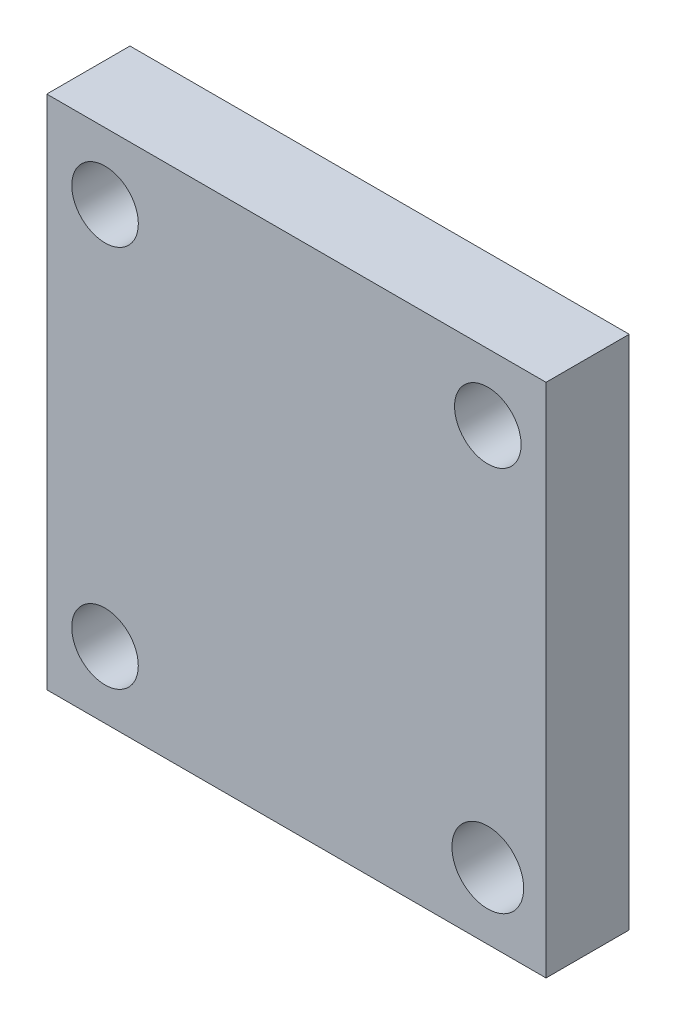
SolidWorks part; units mm, degrees
ref_plane "Front Plane" through (0, 0, 0) normal (0, 0, 1) x (1, 0, 0)
ref_plane "Top Plane" through (0, 0, 0) normal (0, 1, 0) x (1, 0, 0)
ref_plane "Right Plane" through (0, 0, 0) normal (1, 0, 0) x (0, 0, -1)
sketch "Sketch2" plane through (0, 0, 0) normal (0, 0, 1) x (1, 0, 0)
  line L0 (15.0011, -15.5011) -> (-15.0011, -15.5011)
  line L1 (15.0011, -15.5011) -> (15.0011, 15.5011)
  line L2 (15.0011, 15.5011) -> (-15.0011, 15.5011)
  line L3 (-15.0011, -15.5011) -> (-15.0011, 15.5011)
  circle A0 centre (-11.4989, 11.5033) radius 2
  circle A1 centre (11.5033, 11.5011) radius 2
  circle A2 centre (-11.5011, -11.4989) radius 2
  circle A3 centre (11.5011, -11.5011) radius 2.1563
  dimension "D1" = 4
  dimension "D2" = 4
  dimension "D3" = 4
  dimension "D4" = 4.3125
extrude "Boss-Extrude1" add sketch "Sketch2" along normal blind 5
